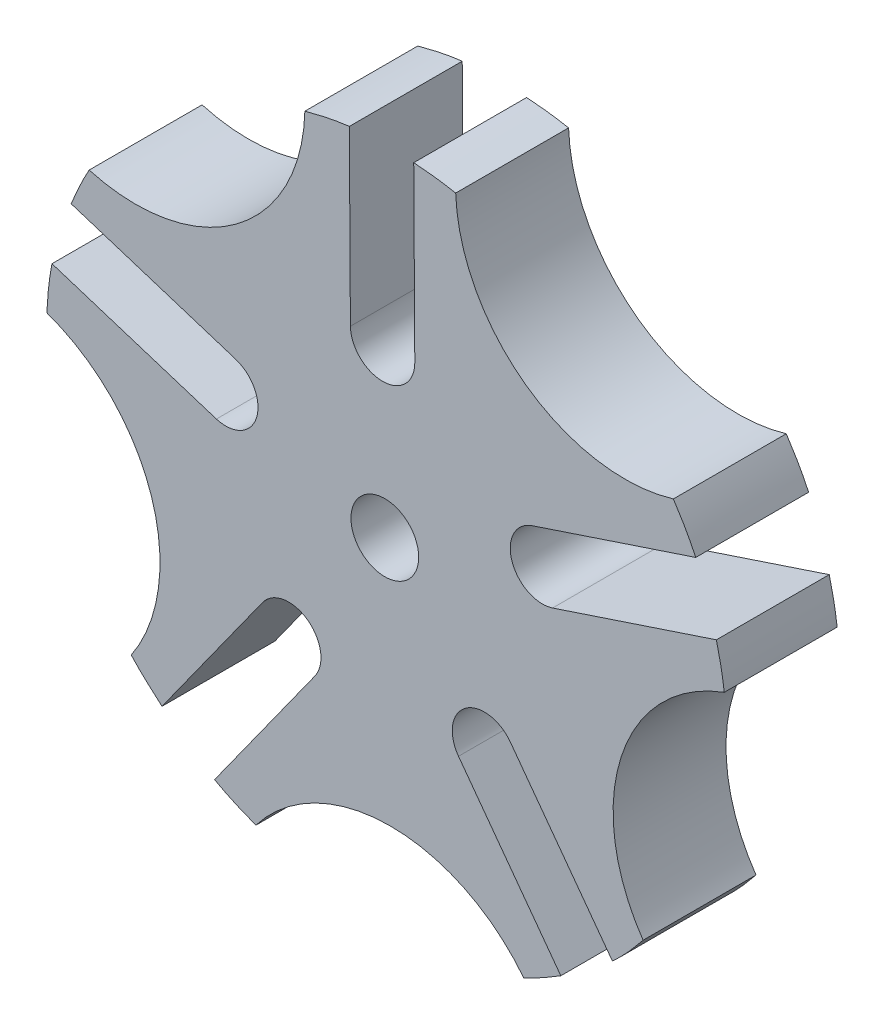
SolidWorks part; units mm, degrees
ref_plane "Front Plane" through (0, 0, 0) normal (0, 0, 1) x (1, 0, 0)
ref_plane "Top Plane" through (0, 0, 0) normal (0, 1, 0) x (1, 0, 0)
ref_plane "Right Plane" through (0, 0, 0) normal (1, 0, 0) x (0, 0, -1)
sketch "Model" plane through (0, 0, 0) normal (0, 0, 1) x (1, 0, 0)
  line L0 (-15.078, -26.0997) -> (-6.1715, -13.6793)
  line L1 (-10.8263, -10.3817) -> (-19.7328, -22.8021)
  line L2 (20.1629, -22.4053) -> (11.1026, -10.0966)
  line L3 (6.5281, -13.5045) -> (15.5884, -25.8132)
  line L4 (-29.4817, 6.2748) -> (-14.9169, 1.6423)
  line L5 (-13.2191, 7.0883) -> (-27.7839, 11.7207)
  line L6 (-3.1426, 29.9777) -> (-3.0476, 14.6943)
  line L7 (2.6564, 14.7625) -> (2.5614, 30.0459)
  line L8 (27.5394, 12.2525) -> (13.0333, 7.4392)
  line L9 (14.8608, 2.0355) -> (29.3669, 6.8487)
  line L10 (0, 0) -> (8.8252, -11.8137) construction
  line L15 (-1.4964, -22.4969) -> (-1.596, -22.5175)
  line L16 (0, 0) -> (0, -17.5109) construction
  line L17 (-29.9561, 0) -> (29.0537, 0) construction
  arc A0 (12.3042, -27.6146) -> (-11.4192, -27.7649) centre (0.5007, -36.8708) ccw
  arc A1 (-10.8263, -10.3817) -> (-6.1715, -13.6793) centre (-8.5083, -12.0438) cw
  arc A2 (-22.4608, -20.2354) -> (-29.9348, 2.2804) centre (-34.9115, -11.8699) ccw
  arc A3 (30.0652, 3.1686) -> (22.8773, -19.4401) centre (35.221, -10.9175) ccw
  circle A4 centre (0, 0) radius 3
  arc A6 (6.5281, -13.5045) -> (11.1026, -10.0966) centre (8.8252, -11.8137) cw
  arc A7 (-13.2191, 7.0883) -> (-14.9169, 1.6423) centre (-14.0836, 4.3702) cw
  arc A8 (-26.1858, 15.1085) -> (-7.0815, 29.1743) centre (-22.0772, 29.5348) ccw
  arc A9 (2.6564, 14.7625) -> (-3.0476, 14.6943) centre (-0.1958, 14.7448) cw
  arc A10 (6.2772, 29.5729) -> (25.5581, 15.7503) centre (21.267, 30.1234) ccw
  arc A11 (14.8608, 2.0355) -> (13.0333, 7.4392) centre (13.9626, 4.7426) cw
  spline S0 degree 3 poles (-7.0815, 29.1743) (-5.7775, 29.5378) (-4.4692, 29.8188) (-3.1426, 29.9777) knots 0 0 0 0 0.021616 0.021616 0.021616 0.021616
  spline S1 degree 3 poles (2.5614, 30.0459) (3.8104, 29.9559) (5.052, 29.8154) (6.2772, 29.5729) knots 0.05229 0.05229 0.05229 0.05229 0.072432 0.072432 0.072432 0.072432
  spline S2 degree 3 poles (25.5581, 15.7503) (26.3068, 14.6224) (26.9783, 13.465) (27.5394, 12.2525) knots 0.2 0.2 0.2 0.2 0.221616 0.221616 0.221616 0.221616
  spline S3 degree 3 poles (29.3669, 6.8487) (29.6672, 5.633) (29.9173, 4.4088) (30.0652, 3.1686) knots 0.25229 0.25229 0.25229 0.25229 0.272432 0.272432 0.272432 0.272432
  spline S4 degree 3 poles (22.8773, -19.4401) (22.0359, -20.5006) (21.1427, -21.4969) (20.1629, -22.4053) knots 0.4 0.4 0.4 0.4 0.421616 0.421616 0.421616 0.421616
  spline S5 degree 3 poles (15.5884, -25.8132) (14.525, -26.4745) (13.438, -27.0907) (12.3042, -27.6146) knots 0.45229 0.45229 0.45229 0.45229 0.472432 0.472432 0.472432 0.472432
  spline S6 degree 3 poles (-11.4192, -27.7649) (-12.6878, -27.2925) (-13.9114, -26.7509) (-15.078, -26.0997) knots 0.6 0.6 0.6 0.6 0.621616 0.621616 0.621616 0.621616
  spline S7 degree 3 poles (-19.7328, -22.8021) (-20.6903, -21.9951) (-21.6122, -21.1517) (-22.4608, -20.2354) knots 0.65229 0.65229 0.65229 0.65229 0.672432 0.672432 0.672432 0.672432
  spline S8 degree 3 poles (-29.9348, 2.2804) (-29.8774, 3.633) (-29.7404, 4.964) (-29.4817, 6.2748) knots 0.8 0.8 0.8 0.8 0.821616 0.821616 0.821616 0.821616
  spline S9 degree 3 poles (-27.7839, 11.7207) (-27.3123, 12.8808) (-26.795, 14.0182) (-26.1858, 15.1085) knots 0.85229 0.85229 0.85229 0.85229 0.872432 0.872432 0.872432 0.872432
  point P60 (0, 0)
  point P77 (0, 0)
  dimension "D1" = 5
extrude "Boss-Extrude3" add sketch "Model" along normal blind 10 contours S9 L5 A7 L4 S8 A2 S7 L1 A1 L0 S6 A0 S5 L3 A6 L2 S4 A3 S3 L9 A11 L8 S2 A10 S1 L7 A9 L6 S0 A8 A4
sketch "Sketch2" plane through (0, 0, 0) normal (0, 0, 1) x (1, 0, 0)
  line L1 (-2.4023, 4.2707) -> (-4.8997, 0.0549)
  line L2 (-4.8997, 0.0549) -> (-2.4974, -4.2158)
  line L3 (-2.4974, -4.2158) -> (2.4023, -4.2707)
  line L4 (2.4023, -4.2707) -> (4.8997, -0.0549)
  line L5 (4.8997, -0.0549) -> (2.4974, 4.2158)
  line L6 (2.4974, 4.2158) -> (-2.4023, 4.2707)
  circle A0 centre (0, 0) radius 4.2435 construction
extrude "Cut-Extrude1" cut sketch "Sketch2" against normal blind 3 and the other way blind 3
